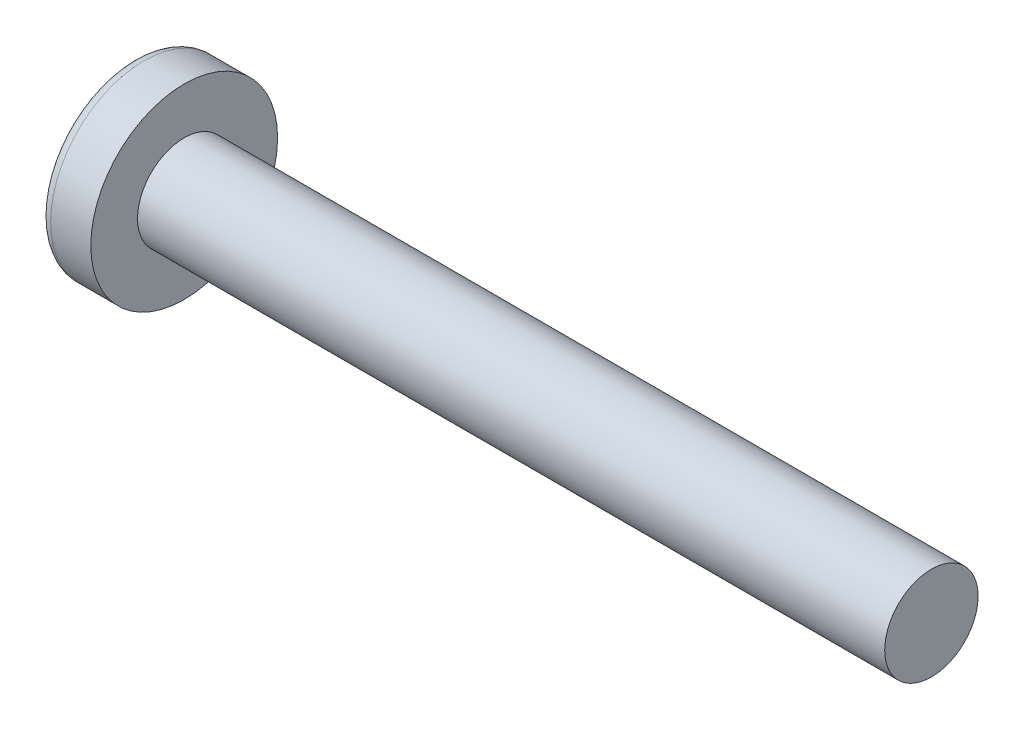
SolidWorks part; units mm, degrees
ref_plane "Plane1" through (0, 0, 0) normal (0, 0, 1) x (1, 0, 0)
ref_plane "Plane2" through (0, 0, 0) normal (0, 1, 0) x (1, 0, 0)
ref_plane "Plane3" through (0, 0, 0) normal (1, 0, 0) x (0, 0, -1)
other "Configuration Table"
sketch "BodySke" plane through (0, 0, 0) normal (0, 0, 1) x (1, 0, 0)
  line L0 (2.1, 1.25) -> (2.1, 2.5)
  line L1 (2.55, 6.35) -> (2.55, -3.175) construction
  line L2 (-25.4, 0) -> (127, 0) construction
  line L3 (22.1, 0) -> (0, 0)
  line L4 (2.1, 1.25) -> (22.1, 1.25)
  line L5 (22.1, 1.25) -> (22.1, 0)
  line L6 (1.0251, 2.5) -> (2.1, 2.5)
  line L7 (2.1, -1.25) -> (22.1, -1.25) construction
  line L8 (2.1, 6.35) -> (2.1, -3.175) construction
  arc A0 (0.7839, 2.3784) -> (0, 0) centre (4, 0) ccw
  arc A2 (0.7839, 2.3784) -> (1.0251, 2.5) centre (1.0251, 2.2) cw
  dimension "Head_crown_rad" = 4
  dimension "Head_fillet_rad" = 0.3
  dimension "Diameter" = 2.5
  dimension "Length" = 20
  dimension "Head_ht" = 2.1
  dimension "Head_dia" = 5
  dimension "Advance" = 0.45
  dimension "Thread_nom" = 20
revolve "Base-Revolve" add sketch "BodySke" angle 360 about L2
cosmetic thread "ThreadCosmetic" [suppressed] parameters "Thread_length"=19.55, "Thread_minor"=1.993
sketch "Sketch3" plane through (0, 0, 0) normal (1, 0, 0) x (0, 0, -1)
  line L0 (0.35, -1.34) -> (-0.35, -1.34)
  line L1 (0.35, -1.34) -> (0.35, 1.34)
  line L2 (-0.35, 1.34) -> (0.35, 1.34)
  line L3 (-0.35, 1.34) -> (-0.35, -1.34)
  dimension "Cross_dia" = 2.68
  dimension "D1" = 1.34
  dimension "Cross_width" = 0.7
  dimension "D2" = 0.35
ref_plane "Plane4" through (1.53, 0, 0) normal (1, 0, 0) x (0, 0, -1)
sketch "Sketch4" plane through (1.53, 0, 0) normal (1, 0, 0) x (0, 0, -1)
  line L0 (0.175, -0.175) -> (-0.175, -0.175)
  line L1 (0.175, -0.175) -> (0.175, 0.175)
  line L2 (-0.175, 0.175) -> (0.175, 0.175)
  line L3 (-0.175, 0.175) -> (-0.175, -0.175)
  dimension "D2" = 0.35
  dimension "D1" = 0.35
  dimension "D3" = 0.175
  dimension "D4" = 0.175
loft "Cut-Loft1" cut profiles "Sketch3", "Sketch4"
pattern_circular "CirPattern1" count 2 every 90 about axis through (0, 0, 0) along (1, 0, 0) of "Cut-Loft1"
sketch "ThdSchSke" plane through (0, 0, 0) normal (0, 0, 1) x (1, 0, 0)
  line L0 (2.55, -0.9965) -> (2.3725, -1.25)
  line L1 (2.55, -0.9965) -> (2.7275, -1.25)
  line L2 (2.7275, -1.25) -> (2.7275, -1.5625)
  line L3 (-3.175, 0) -> (5.1513, 0) construction
  line L5 (2.7275, -1.5625) -> (2.3725, -1.5625)
  line L6 (2.3725, -1.5625) -> (2.3725, -1.25)
  dimension "Diameter" = 2.5
  dimension "SideAngle" = 55
  dimension "VeeAngle" = 70
  dimension "Thread_minor" = 1.993
  dimension "Overcut" = 3.125
  dimension "Start" = 2.55
revolve "ThreadSchematic" [suppressed] cut sketch "ThdSchSke" angle 360 about L3
pattern_linear "ThdSchPat" [suppressed]
equation "\"D1@Sketch3\" = \"Cross_dia@Sketch3\" / 2"
equation "\"D2@Sketch3\" = \"Cross_width@Sketch3\" / 2"
equation "\"D1@Sketch4\" = \"Cross_width@Sketch3\" *.5"
equation "\"D2@Sketch4\" = \"D1@Sketch4\""
equation "\"D3@Sketch4\" = \"D1@Sketch4\" / 2"
equation "\"D4@Sketch4\" = \"D2@Sketch4\" / 2"
equation "\"Thread_length@ThreadCosmetic\" = ((sgn( (\"Length@BodySke\" - \"Advance@BodySke\" ) - \"Thread_nom@BodySke\" )-1)*( (\"Length@BodySke\" - \"Advance@BodySke\" ) - \"Thread_nom@BodySke\" ))/-2+ \"Thread_nom@BodySke\""
equation "\"Thread_minor@ThdSchSke\" = \"Thread_minor@ThreadCosmetic\""
equation "\"Diameter@ThdSchSke\" = \"Diameter@BodySke\""
equation "\"Overcut@ThdSchSke\" = \"Diameter@BodySke\" * 1.25"
equation "\"Start@ThdSchSke\" = \"Head_ht@BodySke\" + \"Length@BodySke\" - \"Thread_length@ThreadCosmetic\"  '---Non-countersunk---"
equation "\"Num_threads@ThdSchPat\" = int( \"Thread_length@ThreadCosmetic\" / \"Advance@BodySke\" + 0.999 )  + 1"
equation "\"Advance@ThdSchPat\" = \"Thread_length@ThreadCosmetic\" /  (\"Num_threads@ThdSchPat\" - 1) 'relax it"
